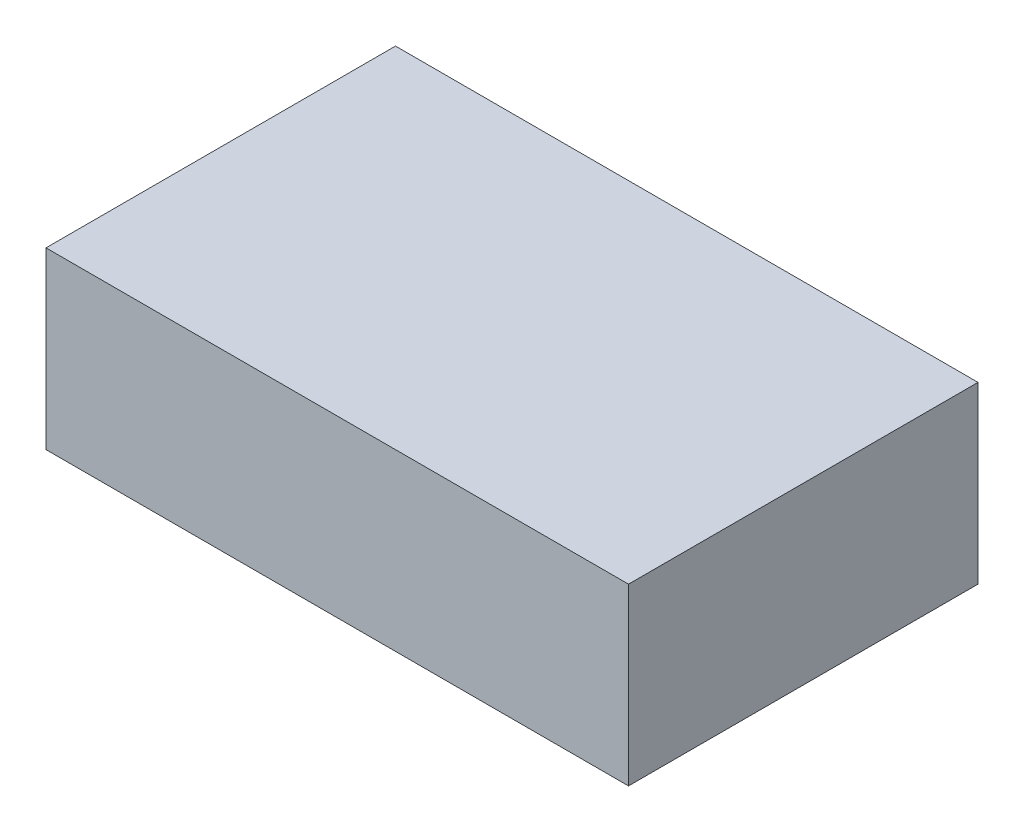
SolidWorks part; units mm, degrees
ref_plane "Front Plane" through (0, 0, 0) normal (0, 0, 1) x (1, 0, 0)
ref_plane "Top Plane" through (0, 0, 0) normal (0, 1, 0) x (1, 0, 0)
ref_plane "Right Plane" through (0, 0, 0) normal (1, 0, 0) x (0, 0, -1)
sketch "Sketch1" plane through (0, 0, 0) normal (0, 1, 0) x (1, 0, 0)
  line L1 (0, 0) -> (-63.5, 0)
  line L2 (0, 0) -> (0, 38.1)
  line L3 (0, 38.1) -> (-63.5, 38.1)
  line L4 (-63.5, 0) -> (-63.5, 38.1)
  dimension "D1" = 63.5
  dimension "D2" = 38.1
extrude "Boss-Extrude1" add sketch "Sketch1" along normal blind 19.05
